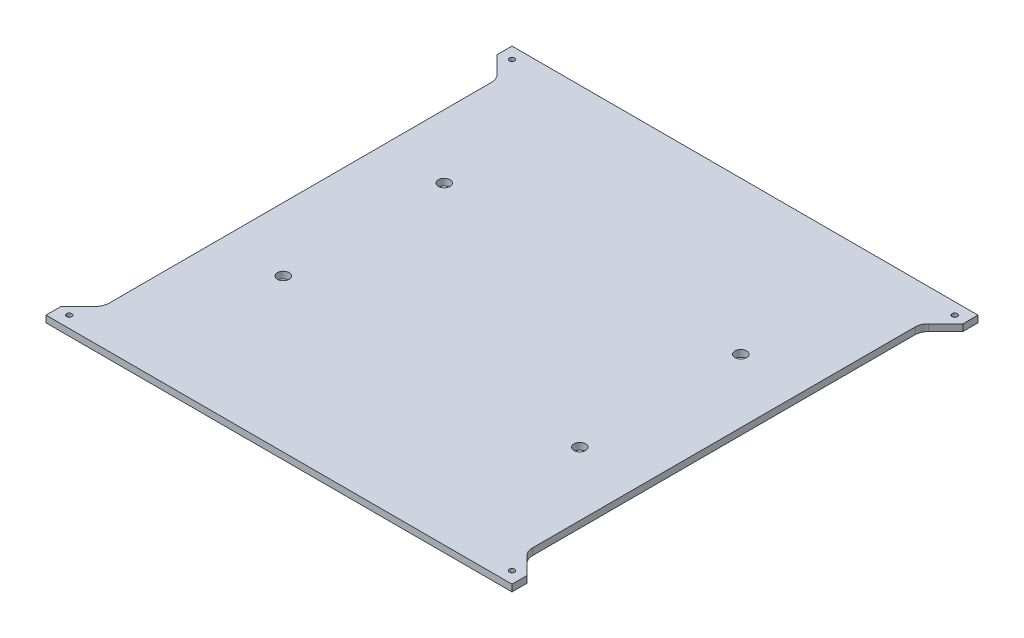
SolidWorks part; units mm, degrees
material "6061-T6 (SS)"
ref_plane "Front Plane" through (0, 0, 0) normal (0, 0, 1) x (1, 0, 0)
ref_plane "Top Plane" through (0, 0, 0) normal (0, 1, 0) x (1, 0, 0)
ref_plane "Right Plane" through (0, 0, 0) normal (1, 0, 0) x (0, 0, -1)
sketch "Sketch1" plane through (0, 0, 0) normal (0, 1, 0) x (1, 0, 0)
  line L0 (-110, 110) -> (110, -110) construction
  line L1 (-110, 110) -> (110, 110)
  line L2 (-110, 110) -> (-110, -110)
  line L3 (-110, -110) -> (110, -110)
  line L4 (110, 110) -> (110, -110)
  point P10 (110, 110)
  point P16 (-110, -110)
  dimension "D1" = 220
  dimension "D2" = 220
extrude "Boss-Extrude1" add sketch "Sketch1" along normal blind 3.175
hole_wizard "M3x0.5 Tapped Hole1" positions "Sketch3" profile "Sketch2" tap size "M3x0.5" standard "Ansi Metric" end condition through all
sketch "Sketch3" plane through (0, 3.175, 0) normal (0, 1, 0) x (-1, 0, 0)
  line L0 (-104.5, 104.5) -> (104.5, -104.5) construction
  point P0 (104.5, -104.5)
  point P1 (-104.5, -104.5)
  point P3 (-104.5, 104.5)
  point P5 (104.5, 104.5)
  dimension "D1" = 209
  dimension "D2" = 209
sketch "Sketch2" plane through (-104.5, 3.175, -104.5) normal (1, 0, 0) x (0, 0, 1)
  line L0 (0, 0) -> (0, 3.175)
  line L1 (0, 3.175) -> (1.25, 3.175)
  line L2 (1.25, 3.175) -> (1.25, 0)
  line L5 (1.25, 0) -> (0, 0)
  line L11 (0, -6.35) -> (0, 107.95) construction
  dimension "Thru Tap Drill Dia." = 2.5
  dimension "Thru Tap Drill Depth" = 3.175
cosmetic thread "Hole Thread1" parameters "D2"=3
cosmetic thread "Hole Thread2" parameters "D2"=3
cosmetic thread "Hole Thread3" parameters "D2"=3
cosmetic thread "Hole Thread4" parameters "D2"=3
sketch "Sketch4" plane through (0, 3.175, 0) normal (0, 1, 0) x (1, 0, 0)
  line L0 (70, 38) -> (-70, -38) construction
  circle A0 centre (-70, 38) radius 2.75
  circle A1 centre (-70, -38) radius 2.75
  circle A2 centre (70, -38) radius 2.75
  circle A3 centre (70, 38) radius 2.75
  dimension "D1" = 5.5
  dimension "D2" = 140
  dimension "D3" = 76
extrude "Cut-Extrude1" cut sketch "Sketch4" against normal through all
sketch "Sketch5" plane through (0, 3.175, 0) normal (0, 1, 0) x (1, 0, 0)
  line L0 (-110, 110) -> (110, -110) construction
  line L1 (-110, -110) -> (110, 110) construction
  line L2 (-110, 0) -> (110, 0) construction
  line L3 (-110, 110) -> (-110, -110) construction
  line L4 (110, -110) -> (110, 110) construction
  line L5 (-72.0888, 79.1599) -> (-4.4901, 11.5612) construction
  line L6 (4.4901, 11.5612) -> (72.0888, 79.1599) construction
  line L7 (67.5987, 90) -> (-67.5987, 90) construction
  line L8 (-4.4901, -11.5612) -> (-72.0888, -79.1599) construction
  line L9 (-67.5987, -90) -> (67.5987, -90) construction
  line L10 (72.0888, -79.1599) -> (4.4901, -11.5612) construction
  line L11 (-60, -16.35) -> (-60, -37.5987) construction
  line L12 (-49.1599, -42.0888) -> (-27.9112, -20.8401) construction
  line L13 (-32.4013, -10) -> (-53.65, -10) construction
  line L14 (32.4013, -10) -> (53.65, -10) construction
  line L15 (60, -16.35) -> (60, -37.5987) construction
  line L16 (49.1599, -42.0888) -> (27.9112, -20.8401) construction
  line L17 (27.9112, 20.8401) -> (49.1599, 42.0888) construction
  line L18 (60, 37.5987) -> (60, 16.35) construction
  line L19 (53.65, 10) -> (32.4013, 10) construction
  line L20 (-32.4013, 10) -> (-53.65, 10) construction
  line L21 (-60, 16.35) -> (-60, 37.5987) construction
  line L22 (-49.1599, 42.0888) -> (-27.9112, 20.8401) construction
  line L23 (-110, -110) -> (110, -110) construction
  line L24 (110, 110) -> (-110, 110) construction
  line L25 (-110, 102.9289) -> (-110, -102.9289)
  line L26 (-110, -102.9289) -> (-101.8599, -94.7888)
  line L27 (-100, -90.2987) -> (-100, 90.2987)
  line L28 (-101.8599, 94.7888) -> (-110, 102.9289)
  line L29 (110, 102.9289) -> (101.8599, 94.7888)
  line L30 (100, 90.2987) -> (100, -90.2987)
  line L31 (101.8599, -94.7888) -> (110, -102.9289)
  line L32 (110, -102.9289) -> (110, 102.9289)
  circle A0 centre (-70, -38) radius 2.75 construction
  circle A1 centre (70, -38) radius 2.75 construction
  arc A2 (-72.0888, 79.1599) -> (-67.5987, 90) centre (-67.5987, 83.65) cw construction
  arc A3 (72.0888, 79.1599) -> (67.5987, 90) centre (67.5987, 83.65) ccw construction
  arc A4 (-4.4901, 11.5612) -> (4.4901, 11.5612) centre (0, 16.0513) ccw construction
  arc A5 (-4.4901, -11.5612) -> (4.4901, -11.5612) centre (0, -16.0513) cw construction
  arc A6 (67.5987, -90) -> (72.0888, -79.1599) centre (67.5987, -83.65) ccw construction
  arc A7 (-72.0888, -79.1599) -> (-67.5987, -90) centre (-67.5987, -83.65) ccw construction
  arc A8 (60, -37.5987) -> (49.1599, -42.0888) centre (53.65, -37.5987) cw construction
  arc A9 (32.4013, -10) -> (27.9112, -20.8401) centre (32.4013, -16.35) ccw construction
  arc A10 (53.65, -10) -> (60, -16.35) centre (53.65, -16.35) cw construction
  arc A11 (60, 16.35) -> (53.65, 10) centre (53.65, 16.35) cw construction
  arc A12 (49.1599, 42.0888) -> (60, 37.5987) centre (53.65, 37.5987) cw construction
  arc A13 (27.9112, 20.8401) -> (32.4013, 10) centre (32.4013, 16.35) ccw construction
  arc A14 (-32.4013, 10) -> (-27.9112, 20.8401) centre (-32.4013, 16.35) ccw construction
  arc A15 (-60, 37.5987) -> (-49.1599, 42.0888) centre (-53.65, 37.5987) cw construction
  arc A16 (-53.65, 10) -> (-60, 16.35) centre (-53.65, 16.35) cw construction
  arc A17 (-60, -16.35) -> (-53.65, -10) centre (-53.65, -16.35) cw construction
  arc A18 (-27.9112, -20.8401) -> (-32.4013, -10) centre (-32.4013, -16.35) ccw construction
  arc A19 (-60, -37.5987) -> (-49.1599, -42.0888) centre (-53.65, -37.5987) ccw construction
  arc A20 (101.8599, 94.7888) -> (100, 90.2987) centre (106.35, 90.2987) ccw
  arc A21 (100, -90.2987) -> (101.8599, -94.7888) centre (106.35, -90.2987) ccw
  arc A22 (-101.8599, -94.7888) -> (-100, -90.2987) centre (-106.35, -90.2987) ccw
  arc A23 (-100, 90.2987) -> (-101.8599, 94.7888) centre (-106.35, 90.2987) ccw
  point P75 (-17.0711, -10)
  dimension "D11" = 6.35
  dimension "D12" = 6.35
  dimension "D15" = 6.35
  dimension "D1" = 5
  dimension "D2" = 10
  dimension "D3" = 5
  dimension "D4" = 5
  dimension "D5" = 10
  dimension "D6" = 20
  dimension "D7" = 20
  dimension "D8" = 20
  dimension "D9" = 10
  dimension "D10" = 10
  dimension "D13" = 40
  dimension "D14" = 40
extrude "Cut-Extrude2" cut sketch "Sketch5" against normal through all
